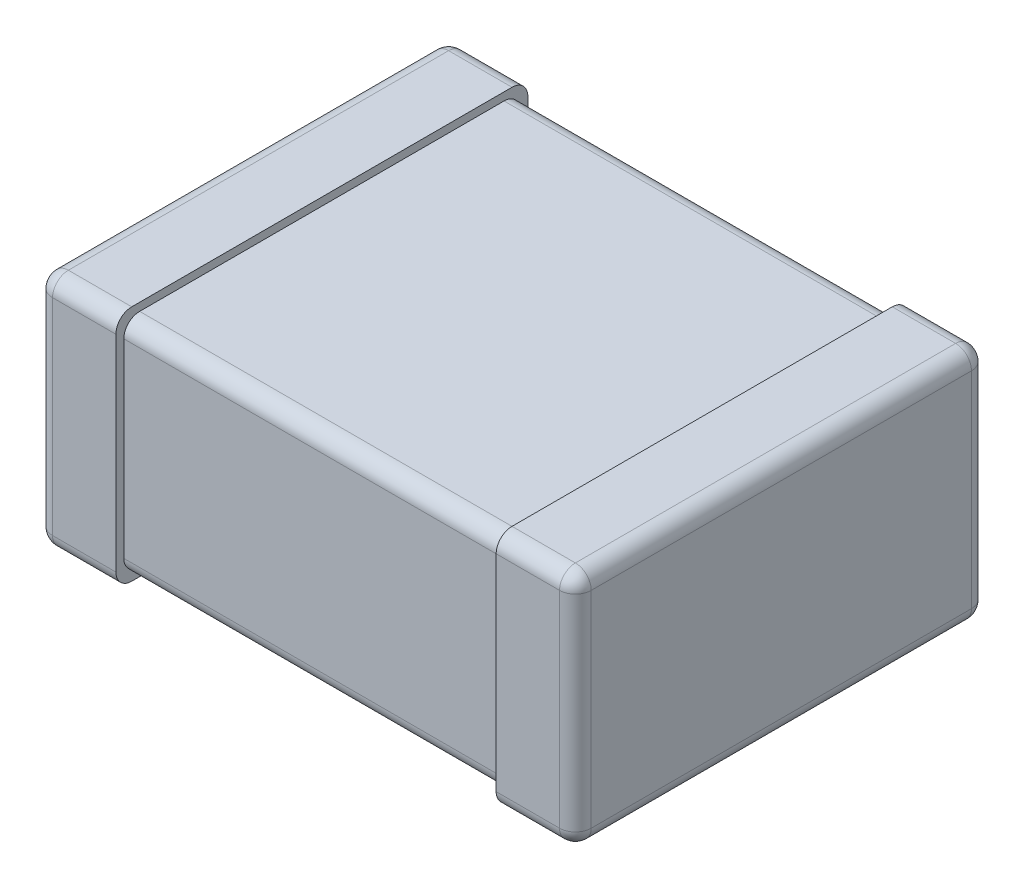
SolidWorks part; units mm, degrees
ref_plane "Front Plane" through (0, 0, 0) normal (0, 0, 1) x (1, 0, 0)
ref_plane "Top Plane" through (0, 0, 0) normal (0, 1, 0) x (1, 0, 0)
ref_plane "Right Plane" through (0, 0, 0) normal (1, 0, 0) x (0, 0, -1)
sketch "Sketch1" plane through (0, 0, 0) normal (0, 1, 0) x (1, 0, 0)
  line L0 (0, 0) -> (3.9337, 0) construction
  line L1 (0, 1.3) -> (0, -1.3) construction
  line L2 (0, 1.3) -> (0, -1.3)
  line L3 (0, -1.3) -> (0.5, -1.3)
  line L4 (0.5, -1.3) -> (0.5, 1.3)
  line L5 (0.5, 1.3) -> (0, 1.3)
  line L6 (0.5, 1.3) -> (3.9337, 1.3) construction
  line L7 (0.5, -1.3) -> (3.9337, -1.3) construction
  line L8 (2.9, 1.3) -> (2.9, -1.3)
  line L9 (2.9, 1.3) -> (3.4, 1.3)
  line L10 (3.4, 1.3) -> (3.4, -1.3)
  line L11 (3.4, -1.3) -> (2.9, -1.3)
  point P5 (0, 0)
  dimension "D1" = 2.6
  dimension "D2" = 2.4
  dimension "D3" = 0.5
extrude "Boss-Extrude1" add sketch "Sketch1" along normal blind 1.5
sketch "Sketch2" plane through (0, 0, 0) normal (0, 1, 0) x (1, 0, 0)
  line L0 (0.5, 1.25) -> (0.5, -1.25)
  line L2 (0.5, -1.25) -> (2.9, -1.25)
  line L3 (2.9, -1.25) -> (2.9, 1.25)
  line L4 (2.9, 1.25) -> (0.5, 1.25)
  line L5 (0, -1.3) -> (0.5, -1.3) construction
  line L6 (0.5, 1.3) -> (0, 1.3) construction
  dimension "D1" = 0.05
  dimension "D2" = 0.05
extrude "Boss-Extrude2" add sketch "Sketch2" along normal blind 1.4 from offset 0.05
fillet "Fillet1" radius 0.1 20 edges at (3.15, 1.5, -1.3) (3.4, 1.5, 0) (3.4, 0.75, 1.3) (3.15, 0, 1.3) (3.15, 0, -1.3) (3.4, 0.75, -1.3) (3.4, 0, 0) (0.25, 1.5, -1.3) (0.25, 0, -1.3) (0, 0.75, -1.3) (0, 0, 0) (0.25, 0, 1.3) (0, 0.75, 1.3) (0.25, 1.5, 1.3) (0, 1.5, 0) (1.7, 0.05, -1.25) (1.7, 1.45, -1.25) (1.7, 0.05, 1.25) (1.7, 1.45, 1.25) (3.15, 1.5, 1.3)
